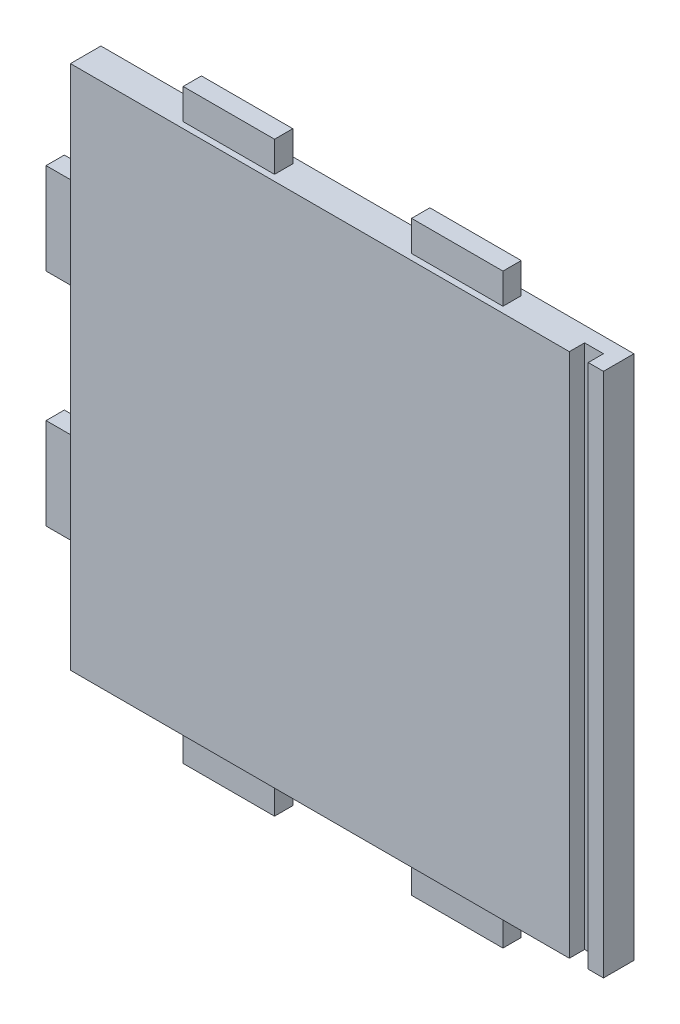
SolidWorks part; units mm, degrees
material "ABS"
ref_plane "Plano frontal" through (0, 0, 0) normal (0, 0, 1) x (1, 0, 0)
ref_plane "Plano superior" through (0, 0, 0) normal (0, 1, 0) x (1, 0, 0)
ref_plane "Plano direito" through (0, 0, 0) normal (1, 0, 0) x (0, 0, -1)
sketch "Esboço1" plane through (0, 0, 0) normal (0, 0, 1) x (1, 0, 0)
  line L1 (87.5, -86.25) -> (-87.5, -86.25)
  line L2 (87.5, -86.25) -> (87.5, 86.25)
  line L3 (87.5, 86.25) -> (-87.5, 86.25)
  line L4 (-87.5, -86.25) -> (-87.5, 86.25)
  line L5 (87.5, -86.25) -> (-87.5, 86.25) construction
  line L6 (87.5, 86.25) -> (-87.5, -86.25) construction
  point P0 (0, 0)
  dimension "D1" = 172.5
  dimension "D2" = 175
extrude "Ressalto-extrusão1" add sketch "Esboço1" along normal blind 10
sketch "Esboço5" plane through (0, 86.25, 0) normal (0, 1, 0) x (1, 0, 0)
  line L0 (0, 0) -> (0, -10) construction
  line L1 (87.5, -10) -> (-87.5, -10) construction
  line L2 (-87.5, -5) -> (87.5, -5) construction
  line L3 (-87.5, -10) -> (-87.5, 0) construction
  line L4 (87.5, -10) -> (87.5, 0) construction
  line L5 (22.5, -2) -> (52.5, -8) construction
  line L6 (-22.5, -8) -> (-52.5, -8)
  line L7 (-22.5, -8) -> (-22.5, -2)
  line L8 (-22.5, -2) -> (-52.5, -2)
  line L9 (-52.5, -8) -> (-52.5, -2)
  line L10 (-22.5, -8) -> (-52.5, -2) construction
  line L11 (-22.5, -2) -> (-52.5, -8) construction
  line L12 (22.5, -8) -> (52.5, -2) construction
  line L13 (52.5, -8) -> (52.5, -2)
  line L14 (22.5, -2) -> (52.5, -2)
  line L15 (22.5, -8) -> (22.5, -2)
  line L16 (22.5, -8) -> (52.5, -8)
  point P11 (-37.5, -5)
  point P20 (37.5, -5)
  dimension "D1" = 30
  dimension "D2" = 6
  dimension "D3" = 50
extrude "Ressalto-extrusão5" add sketch "Esboço5" along normal blind 10
sketch "Esboço6" plane through (-87.5, 0, 0) normal (-1, 0, 0) x (0, 0, 1)
  line L0 (5, 80.8371) -> (5, -100.2795) construction
  line L1 (0, 86.25) -> (0, -86.25) construction
  line L2 (-31.1105, 0) -> (49.0505, 0) construction
  line L3 (10, 86.25) -> (0, 86.25) construction
  line L4 (8, 21.25) -> (2, 21.25)
  line L5 (8, 21.25) -> (8, 51.25)
  line L6 (8, 51.25) -> (2, 51.25)
  line L7 (2, 21.25) -> (2, 51.25)
  line L8 (8, 21.25) -> (2, 51.25) construction
  line L9 (8, 51.25) -> (2, 21.25) construction
  line L10 (8, -51.25) -> (2, -21.25) construction
  line L11 (8, -21.25) -> (2, -51.25) construction
  line L12 (2, -21.25) -> (2, -51.25)
  line L13 (8, -51.25) -> (2, -51.25)
  line L14 (8, -21.25) -> (8, -51.25)
  line L15 (8, -21.25) -> (2, -21.25)
  point P6 (5, 36.25)
  point P19 (5, -36.25)
  dimension "D1" = 5
  dimension "D2" = 6
  dimension "D3" = 30
  dimension "D4" = 50
extrude "Ressalto-extrusão6" add sketch "Esboço6" along normal blind 10
sketch "Esboço7" plane through (0, -86.25, 0) normal (0, -1, 0) x (1, 0, 0)
  line L0 (-118.1326, 5) -> (111.1308, 5) construction
  line L1 (-87.5, 10) -> (87.5, 10) construction
  line L2 (0, -18.9857) -> (0, 24.411) construction
  line L3 (-87.5, 10) -> (-87.5, 0) construction
  line L4 (-22.5, 2) -> (-52.5, 2)
  line L5 (-22.5, 2) -> (-22.5, 8)
  line L6 (-22.5, 8) -> (-52.5, 8)
  line L7 (-52.5, 2) -> (-52.5, 8)
  line L8 (-22.5, 2) -> (-52.5, 8) construction
  line L9 (-22.5, 8) -> (-52.5, 2) construction
  line L10 (22.5, 8) -> (52.5, 2) construction
  line L11 (22.5, 2) -> (52.5, 8) construction
  line L12 (52.5, 2) -> (52.5, 8)
  line L13 (22.5, 8) -> (52.5, 8)
  line L14 (22.5, 2) -> (22.5, 8)
  line L15 (22.5, 2) -> (52.5, 2)
  point P6 (-37.5, 5)
  point P19 (37.5, 5)
  dimension "D1" = 5
  dimension "D2" = 30
  dimension "D3" = 6
  dimension "D4" = 50
extrude "Ressalto-extrusão7" add sketch "Esboço7" along normal blind 10
sketch "Esboço9" plane through (0, 0, 10) normal (0, 0, 1) x (1, 0, 0)
  line L0 (-128.9027, 0) -> (135.2115, 0) construction
  line L1 (87.5, 86.25) -> (-87.5, 86.25) construction
  line L2 (82.5, -86.25) -> (76.3, -86.25)
  line L3 (82.5, -86.25) -> (82.5, 86.25)
  line L4 (82.5, 86.25) -> (76.3, 86.25)
  line L5 (76.3, -86.25) -> (76.3, 86.25)
  line L6 (82.5, -86.25) -> (76.3, 86.25) construction
  line L7 (82.5, 86.25) -> (76.3, -86.25) construction
  line L8 (87.5, -86.25) -> (87.5, 86.25) construction
  point P2 (79.4, 0)
  dimension "D1" = 5
  dimension "D2" = 6.2
extrude "Corte-extrusão2" cut sketch "Esboço9" against normal blind 5
sketch "Esboço10" plane through (-87.5, 0, 0) normal (-1, 0, 0) x (0, 0, 1)
  line L0 (5, 90.017) -> (5, -99.8466) construction
  line L1 (0, 86.25) -> (0, -86.25) construction
  line L2 (10, -86.25) -> (0, -86.25) construction
  line L3 (-7.9793, -71.25) -> (19.2427, -71.25) construction
  circle A1 centre (5, -71.25) radius 1.5
  dimension "D2" = 3
  dimension "D3" = 15
  dimension "D1" = 5
extrude "Corte-extrusão3" cut sketch "Esboço10" against normal blind 8
sketch "Esboço11" plane through (0, -86.25, 0) normal (0, -1, 0) x (1, 0, 0)
  line L0 (-123.7293, 5) -> (109.1351, 5) construction
  line L1 (-87.5, 0) -> (87.5, 0) construction
  line L2 (87.5, 10) -> (87.5, 0) construction
  circle A0 centre (65, 5) radius 1.5
  dimension "D2" = 3
  dimension "D3" = 22.5
  dimension "D1" = 5
extrude "Corte-extrusão4" cut sketch "Esboço11" against normal blind 8
